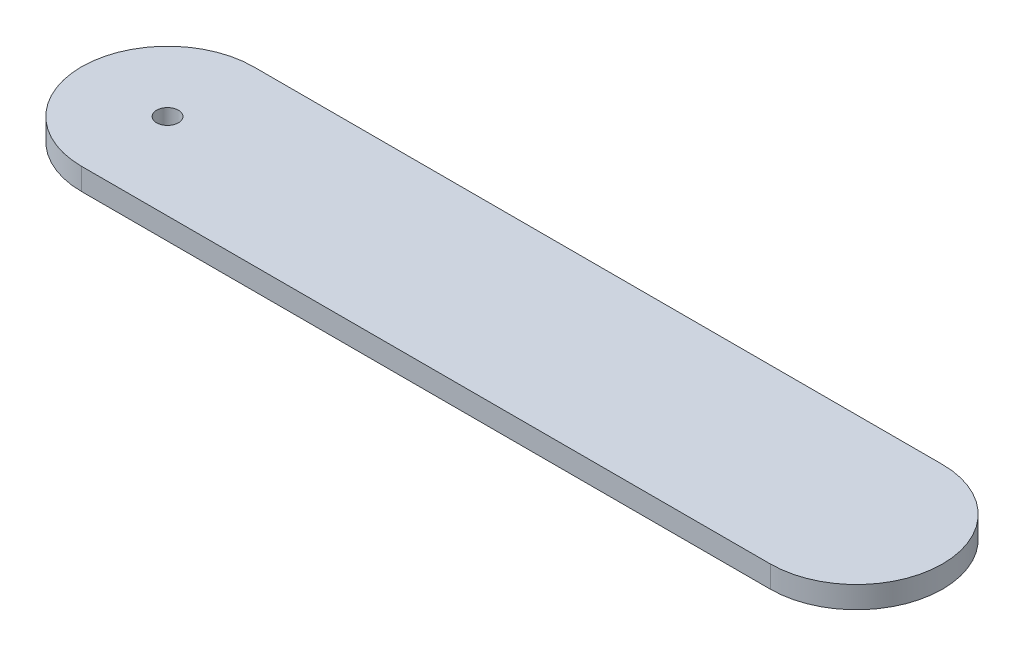
SolidWorks part; units mm, degrees
ref_plane "Front Plane" through (0, 0, 0) normal (0, 0, 1) x (1, 0, 0)
ref_plane "Top Plane" through (0, 0, 0) normal (0, 1, 0) x (1, 0, 0)
ref_plane "Right Plane" through (0, 0, 0) normal (1, 0, 0) x (0, 0, -1)
sketch "Sketch1" plane through (0, 0, 0) normal (0, 1, 0) x (1, 0, 0)
  line L0 (0, 0) -> (200, 0) construction
  line L1 (0, 25) -> (200, 25)
  line L2 (0, -25) -> (200, -25)
  arc A0 (0, 25) -> (0, -25) centre (0, 0) ccw
  arc A1 (200, -25) -> (200, 25) centre (200, 0) ccw
  point P3 (100, 0)
  dimension "D1" = 200
  dimension "D2" = 50
sketch "Sketch2" plane through (0, 0, 0) normal (0, 1, 0) x (1, 0, 0)
  line L0 (0, 25) -> (200, 25)
  line L1 (0, -25) -> (200, -25)
  line L2 (0, 0) -> (200, 0) construction
  arc A0 (0, 25) -> (0, -25) centre (0, 0) ccw
  arc A1 (200, -25) -> (200, 25) centre (200, 0) ccw
  point P2 (100, 0)
extrude "Boss-Extrude1" add sketch "Sketch2" along normal blind 6.35
sketch "Sketch3" plane through (0, 6.35, 0) normal (0, 1, 0) x (1, 0, 0)
  circle A0 centre (0, 0) radius 3.175
  dimension "D1" = 6.35
sketch "Sketch4" plane through (0, 6.35, 0) normal (0, 1, 0) x (1, 0, 0)
  circle A0 centre (0, 0) radius 3.175
extrude "Cut-Extrude1" cut sketch "Sketch4" against normal through all
